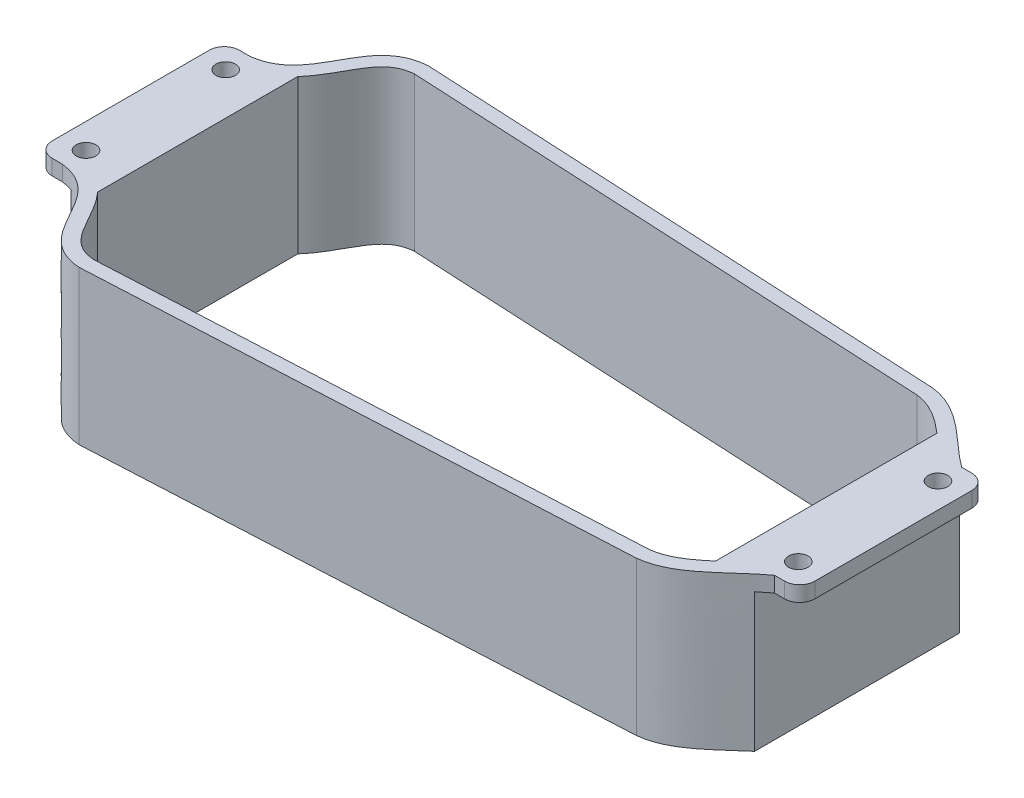
SolidWorks part; units mm, degrees
ref_plane "Front Plane" through (0, 0, 0) normal (0, 0, 1) x (1, 0, 0)
ref_plane "Top Plane" through (0, 0, 0) normal (0, 1, 0) x (1, 0, 0)
ref_plane "Right Plane" through (0, 0, 0) normal (1, 0, 0) x (0, 0, -1)
sketch "Sketch1" plane through (0, 0, 0) normal (0, 1, 0) x (1, 0, 0)
  line L0 (-77.2974, -66.9431) -> (112.638, -57.3431)
  line L2 (-121.2974, 23.6569) -> (-121.2974, -32.5431)
  line L4 (151.7026, 23.6569) -> (151.7026, -32.5431)
  line L5 (-115.7974, -37.9431) -> (-115.8974, -37.9431)
  line L6 (-115.7974, -37.9431) -> (-112.2974, -37.9431)
  line L7 (-77.2974, 58.0569) -> (112.638, 48.4569)
  line L8 (146.2026, -37.9431) -> (142.7026, -37.9431)
  line L9 (-115.7974, 29.0569) -> (-112.2974, 29.0569)
  line L10 (-115.7974, 29.0569) -> (-115.8974, 29.0569)
  line L11 (146.2026, 29.0569) -> (142.7026, 29.0569)
  line L12 (146.2026, 29.0569) -> (146.3026, 29.0569)
  line L13 (146.2026, -37.9431) -> (146.3026, -37.9431)
  circle A0 centre (-112.2974, 20.5569) radius 3.5
  circle A1 centre (-112.2974, -29.4431) radius 3.5
  circle A2 centre (142.7026, -29.4431) radius 3.5
  circle A3 centre (142.7026, 20.5569) radius 3.5
  arc A4 (-115.8974, -37.9431) -> (-121.2974, -32.5431) centre (-115.8974, -32.5431) cw
  arc A5 (-115.8974, 29.0569) -> (-121.2974, 23.6569) centre (-115.8974, 23.6569) ccw
  arc A6 (146.3026, -37.9431) -> (151.7026, -32.5431) centre (146.3026, -32.5431) ccw
  arc A7 (146.3026, 29.0569) -> (151.7026, 23.6569) centre (146.3026, 23.6569) cw
  spline S0 degree 3 poles (-77.2974, 58.0569) (-97.4783, 56.5585) (-92.6699, 31.2994) (-112.2974, 29.0569) knots 0 0 0 0 1 1 1 1
  spline S1 degree 3 poles (-77.2974, -66.9431) (-97.4783, -65.4448) (-92.6699, -40.1856) (-112.2974, -37.9431) knots 0 0 0 0 1 1 1 1
  spline S2 degree 3 poles (112.638, 48.4569) (125.0826, 47.1415) (133.2878, 35.7758) (142.7026, 29.0569) knots 0 0 0 0 1 1 1 1
  spline S3 degree 3 poles (112.638, -57.3431) (125.0826, -56.0277) (133.2878, -44.662) (142.7026, -37.9431) knots 0 0 0 0 1 1 1 1
  point P8 (-121.2974, -4.4431)
  point P25 (-114.0474, 29.0569)
  dimension "D6" = 7
  dimension "D7" = 7
  dimension "D2" = 5.4
  dimension "D3" = 50
  dimension "D4" = 25
  dimension "D5" = 39.0646
  dimension "D12" = 8.5
extrude "Boss-Extrude2" add sketch "Sketch1" against normal blind 55
sketch "Sketch7" plane through (-121.2974, 0, 0) normal (-1, 0, 0) x (0, 0, 1)
  line L0 (-23.6569, 0) -> (32.5431, 0) construction
  line L1 (-30.1667, -5.5) -> (38.8329, -5.5)
  line L2 (-30.1667, -5.5) -> (-30.1667, -55.9156)
  line L3 (-30.1667, -55.9156) -> (38.8329, -55.9156)
  line L4 (38.8329, -5.5) -> (38.8329, -55.9156)
  dimension "D1" = 68.9997
  dimension "D2" = 5.5
extrude "Cut-Extrude5" cut sketch "Sketch7" against normal blind 13
sketch "Sketch19" plane through (151.7026, 0, 0) normal (1, 0, 0) x (0, 0, -1)
  line L0 (-32.5431, 0) -> (23.6569, 0) construction
  line L1 (-42.5272, -5.5) -> (32.3322, -5.5)
  line L2 (-42.5272, -5.5) -> (-42.5272, -66.2251)
  line L3 (-42.5272, -66.2251) -> (32.3322, -66.2251)
  line L4 (32.3322, -5.5) -> (32.3322, -66.2251)
  dimension "D1" = 5.5
extrude "Cut-Extrude7" cut sketch "Sketch19" against normal blind 13
sketch "Sketch24" plane through (0, 0, 0) normal (0, 1, 0) x (1, 0, 0)
  line L0 (-121.2974, 23.6569) -> (-121.2974, -32.5431) construction
  line L1 (151.7026, -32.5431) -> (151.7026, 23.6569) construction
  line L2 (-108.2974, -38.8081) -> (-108.2974, 29.9219) construction
  line L3 (138.7026, 32.1977) -> (138.7026, -41.0839) construction
  line L24 (-97.2974, 31.3724) -> (-97.2974, -40.2586)
  line L25 (127.7026, -44.0855) -> (127.7026, 35.1992)
  line L32 (-115.8974, -32.9431) -> (-112.0127, -32.9431)
  line L33 (-77.2198, -61.9328) -> (112.2401, -52.3569)
  line L34 (141.1014, -32.9431) -> (146.3026, -32.9431)
  line L35 (146.7026, -32.5431) -> (146.7026, 23.6569)
  line L36 (146.3026, 24.0569) -> (141.1014, 24.0569)
  line L37 (112.2401, 43.4706) -> (-77.2198, 53.0466)
  line L38 (-112.0127, 24.0569) -> (-115.8974, 24.0569)
  line L39 (-116.2974, 23.6569) -> (-116.2974, -32.5431)
  line L41 (-77.2198, -61.9328) -> (112.2401, -52.3569)
  line L45 (112.2401, 43.4706) -> (-77.2198, 53.0466)
  arc A16 (-116.2974, -32.5431) -> (-115.8974, -32.9431) centre (-115.8974, -32.5431) ccw
  arc A17 (146.3026, -32.9431) -> (146.7026, -32.5431) centre (146.3026, -32.5431) ccw
  arc A18 (146.7026, 23.6569) -> (146.3026, 24.0569) centre (146.3026, 23.6569) ccw
  arc A19 (-115.8974, 24.0569) -> (-116.2974, 23.6569) centre (-115.8974, 23.6569) ccw
  spline S16 degree 3 poles (916.7028, 3831.6477) (-169.2941, -66.3151) (-134.6648, -29.9567) (-111.0199, -33.0648) (-110.2801, -33.1724) (-109.549, -33.311) (-108.0991, -33.6313) (-107.149, -33.9026) (-105.751, -34.4049) (-105.2895, -34.5883) (-104.3761, -34.9886) (-103.9225, -35.2064) (-102.5894, -35.9057) (-101.7446, -36.4289) (-100.1371, -37.5819) (-99.3744, -38.2117) (-98.287, -39.23) (-97.934, -39.5816) (-97.2457, -40.3081) (-96.9107, -40.6828) (-95.296, -42.5861) (-94.1801, -44.2218) (-92.115, -47.6003) (-91.1676, -49.3443) (-89.7143, -51.9397) (-89.224, -52.8014) (-88.1974, -54.4933) (-87.6614, -55.3236) (-86.7872, -56.5206) (-86.4839, -56.9115) (-85.8453, -57.671) (-85.5107, -58.0385) (-84.4614, -59.081) (-83.6971, -59.7) (-82.4171, -60.4721) (-81.9757, -60.6988) (-81.0738, -61.0903) (-80.6119, -61.2559) (-36.0382, -74.3841) (101.9888, 146.3212) (-3586.8347, -1978.4439) knots -1.461001 -1.461001 -1.461001 -1.461001 0.015625 0.015625 0.03125 0.0625 0.0625 0.125 0.125 0.15625 0.15625 0.1875 0.1875 0.25 0.25 0.3125 0.3125 0.34375 0.34375 0.375 0.375 0.5 0.5 0.625 0.625 0.6875 0.6875 0.75 0.75 0.78125 0.78125 0.8125 0.8125 0.875 0.875 0.90625 0.90625 0.9375 0.9375 3.859593 3.859593 3.859593 3.859593 only from (-112.0127, -32.9431) to (-77.2198, -61.9328)
  spline S17 degree 3 poles (-1325.1696, 3676.6477) (-92.5659, 179.5709) (57.6605, -72.8599) (117.1824, -51.088) (117.8533, -50.8014) (119.1741, -50.1652) (119.8264, -49.8142) (121.7324, -48.6969) (122.9407, -47.8666) (125.2852, -46.1073) (126.4211, -45.1778) (129.7767, -42.3182) (131.9411, -40.3208) (135.2709, -37.4274) (136.3945, -36.4794) (138.1252, -35.1119) (138.7097, -34.6652) (139.6012, -34.0129) (139.9016, -33.7994) (1225.7998, 741.15) (2311.398, 1515.8853) (3396.9984, 2290.6191) knots -5.258001 -5.258001 -5.258001 -5.258001 0.125 0.125 0.1875 0.1875 0.25 0.25 0.375 0.375 0.5 0.5 0.75 0.75 0.875 0.875 0.9375 0.9375 0.96875 0.96875 114.067564 114.067564 114.067564 114.067564 only from (112.2401, -52.3569) to (141.1014, -32.9431)
  spline S18 degree 3 poles (3396.9877, -2299.5047) (2311.3945, -1524.769) (1225.7994, -750.036) (139.9053, 24.9105) (139.6058, 25.1233) (138.7169, 25.7736) (138.1338, 26.2191) (136.4069, 27.583) (135.2851, 28.529) (131.9604, 31.4172) (129.7998, 33.4111) (126.4482, 36.2691) (125.3123, 37.1997) (123.5488, 38.5245) (122.9505, 38.9544) (121.7356, 39.7768) (121.1181, 40.1699) (119.2278, 41.2805) (117.9177, 41.9303) (115.8367, 42.6953) (115.1306, 42.9121) (44.3541, 60.0309) (-123.771, -340.1781) (-1008.9989, -3790.8931) knots -113.41936 -113.41936 -113.41936 -113.41936 0.03125 0.03125 0.0625 0.0625 0.125 0.125 0.25 0.25 0.5 0.5 0.625 0.625 0.6875 0.6875 0.75 0.75 0.875 0.875 0.9375 0.9375 7.063441 7.063441 7.063441 7.063441 only from (141.1014, 24.0569) to (112.2401, 43.4706)
  spline S19 degree 3 poles (-862.5606, 3972.405) (97.4286, -234.0983) (-29.5529, 67.5536) (-80.6524, 52.3563) (-81.1262, 52.1845) (-82.0533, 51.7752) (-82.4971, 51.5419) (-83.3463, 51.0201) (-83.7517, 50.7316) (-84.528, 50.1044) (-84.8995, 49.765) (-85.9649, 48.6874) (-86.5897, 47.914) (-87.7478, 46.3083) (-88.2803, 45.4755) (-89.3014, 43.7816) (-89.7895, 42.9203) (-91.2394, 40.3269) (-92.1889, 38.5842) (-94.256, 35.221) (-95.3711, 33.6018) (-97.2863, 31.3589) (-97.965, 30.642) (-99.0577, 29.6239) (-99.4328, 29.2957) (-100.1987, 28.6686) (-100.5905, 28.3688) (-101.793, 27.5115) (-102.6308, 26.9961) (-103.9435, 26.31) (-104.3903, 26.0957) (-105.3029, 25.6966) (-105.7669, 25.5126) (-107.1668, 25.0108) (-108.1162, 24.7407) (-109.5618, 24.4222) (-110.2901, 24.2846) (-111.026, 24.1777) (-134.6369, 21.0782) (-167.8592, 57.4575) (789.9971, -3872.1311) knots -3.234881 -3.234881 -3.234881 -3.234881 0.0625 0.0625 0.09375 0.09375 0.125 0.125 0.15625 0.15625 0.1875 0.1875 0.25 0.25 0.3125 0.3125 0.375 0.375 0.5 0.5 0.625 0.625 0.6875 0.6875 0.71875 0.71875 0.75 0.75 0.8125 0.8125 0.84375 0.84375 0.875 0.875 0.9375 0.9375 0.96875 0.984375 0.984375 2.46758 2.46758 2.46758 2.46758 only from (-77.2198, 53.0466) to (-112.0127, 24.0569)
  spline S20 degree 3 poles (-97.2974, -40.2586) (-97.0554, -40.5225) (-96.8185, -40.7915) (-95.296, -42.5861) (-94.1801, -44.2218) (-92.115, -47.6003) (-91.1676, -49.3443) (-89.7143, -51.9397) (-89.224, -52.8014) (-88.1974, -54.4933) (-87.6614, -55.3236) (-86.7872, -56.5206) (-86.4839, -56.9115) (-85.8453, -57.671) (-85.5107, -58.0385) (-84.4614, -59.081) (-83.6971, -59.7) (-82.4171, -60.4721) (-81.9757, -60.6988) (-81.0738, -61.0903) (-80.6119, -61.2559) (-79.197, -61.6727) (-78.2107, -61.8436) (-77.2198, -61.9328) knots 0.352672 0.352672 0.352672 0.352672 0.375 0.375 0.5 0.5 0.625 0.625 0.6875 0.6875 0.75 0.75 0.78125 0.78125 0.8125 0.8125 0.875 0.875 0.90625 0.90625 0.9375 0.9375 1 1 1 1
  spline S21 degree 3 poles (112.2401, -52.3569) (113.7174, -52.1897) (115.133, -51.8377) (117.1824, -51.088) (117.8533, -50.8014) (119.1741, -50.1652) (119.8264, -49.8142) (121.7324, -48.6969) (122.9407, -47.8666) (125.2852, -46.1073) (126.4211, -45.1778) (127.594, -44.1783) (127.6483, -44.1319) (127.7026, -44.0855) knots 0 0 0 0 0.125 0.125 0.1875 0.1875 0.25 0.25 0.375 0.375 0.5 0.5 0.506074 0.506074 0.506074 0.506074
  spline S22 degree 3 poles (127.7026, 35.1992) (127.6569, 35.2383) (126.4947, 36.231) (125.3123, 37.1997) (123.5488, 38.5245) (122.9505, 38.9544) (121.7356, 39.7768) (121.1181, 40.1699) (119.2278, 41.2805) (117.9177, 41.9303) (115.8367, 42.6953) (115.1306, 42.9121) (113.701, 43.2579) (112.976, 43.3873) (112.2401, 43.4706) knots 0.494879 0.494879 0.494879 0.494879 0.5 0.625 0.625 0.6875 0.6875 0.75 0.75 0.875 0.875 0.9375 0.9375 1 1 1 1
  spline S23 degree 3 poles (-77.2198, 53.0466) (-78.2263, 52.9559) (-79.2132, 52.7844) (-80.6524, 52.3563) (-81.1262, 52.1845) (-82.0533, 51.7752) (-82.4971, 51.5419) (-83.3463, 51.0201) (-83.7517, 50.7316) (-84.528, 50.1044) (-84.8995, 49.765) (-85.9649, 48.6874) (-86.5897, 47.914) (-87.7478, 46.3083) (-88.2803, 45.4755) (-89.3014, 43.7816) (-89.7895, 42.9203) (-91.2394, 40.3269) (-92.1889, 38.5842) (-94.256, 35.221) (-95.3711, 33.6018) (-96.8599, 31.8583) (-97.0762, 31.6135) (-97.2974, 31.3724) knots 0 0 0 0 0.0625 0.0625 0.09375 0.09375 0.125 0.125 0.15625 0.15625 0.1875 0.1875 0.25 0.25 0.3125 0.3125 0.375 0.375 0.5 0.5 0.625 0.625 0.645749 0.645749 0.645749 0.645749
  dimension "D2" = 24
  dimension "D3" = 24
  dimension "D1" = 5
extrude "Cut-Extrude9" cut sketch "Sketch24" against normal blind 55
